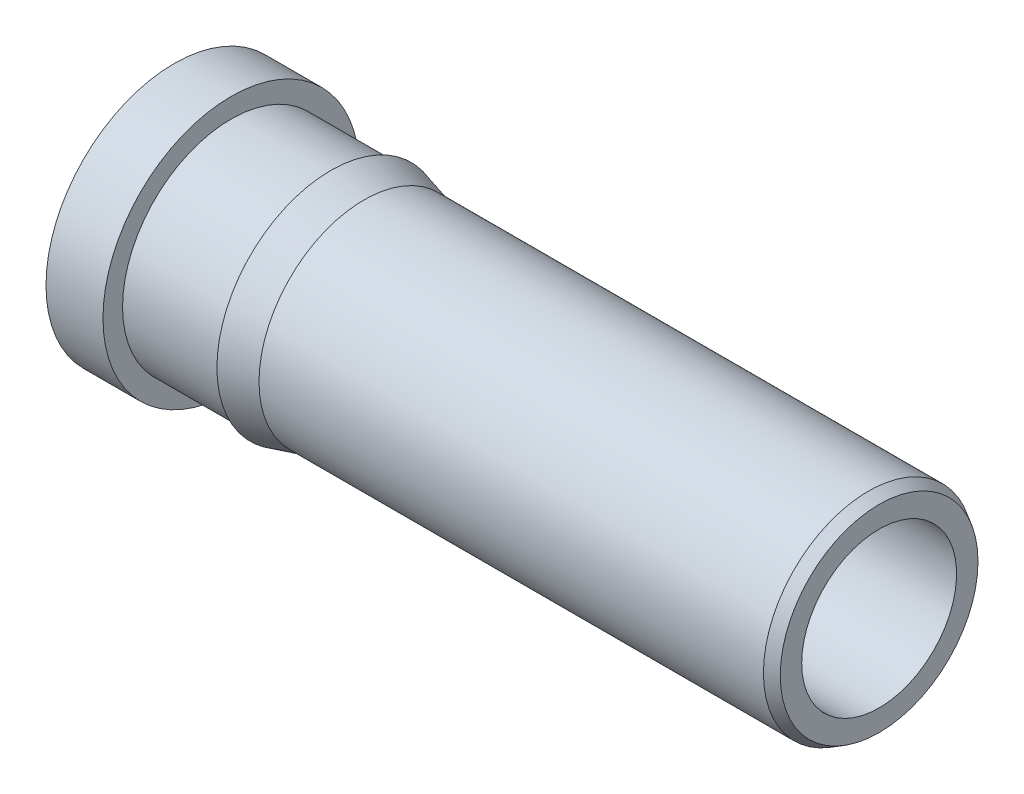
SolidWorks part; units mm, degrees
material "Brass Alloy 385"
ref_plane "Front Plane" through (0, 0, 0) normal (0, 0, 1) x (1, 0, 0)
ref_plane "Top Plane" through (0, 0, 0) normal (0, 1, 0) x (1, 0, 0)
ref_plane "Right Plane" through (0, 0, 0) normal (1, 0, 0) x (0, 0, -1)
sketch "Sketch1" plane through (0, 0, 0) normal (0, 0, 1) x (1, 0, 0)
  line L0 (0, 0) -> (0, 0.9144)
  line L1 (0, 0.9144) -> (0.4064, 0.9144)
  line L2 (0.4064, 0.9144) -> (0.4064, 0.7747)
  line L3 (0.4064, 0.7747) -> (1.1176, 0.7747)
  line L4 (1.1176, 0.7747) -> (1.1176, 0.8128)
  line L5 (1.1176, 0.8128) -> (1.3546, 0.7493)
  line L6 (1.3546, 0.7493) -> (4.953, 0.7493)
  line L7 (4.953, 0.7493) -> (5.0292, 0.7053)
  line L8 (5.0292, 0.7053) -> (5.0292, 0)
  line L9 (0, 0) -> (5.0292, 0)
  line L10 (0, 0) -> (5.0292, 0) construction
revolve "RevolutionAngle1" add sketch "Sketch1" angle 360 about L10
hole_wizard "Hole1" positions "Sketch3" profile "Sketch2" legacy
sketch "Sketch3" plane through (0, 0, 0) normal (-1, 0, 0) x (0, 0, 1)
  point P0 (0, 0)
sketch "Sketch2" plane through (0, 0, 0) normal (0, 1, 0) x (0, 0, 1)
  line L0 (0, 0) -> (0, 2.726)
  line L1 (0, 2.726) -> (0.6477, 2.3368)
  line L2 (0.6477, 2.3368) -> (0.6477, 0)
  line L4 (0.6477, 0) -> (0, 0)
  line L6 (0, 2.726) -> (-0.6477, 2.3368) construction
  line L7 (0, -4.2442) -> (0, 117.3081) construction
  dimension "Diameter" = 1.2954
  dimension "Depth" = 2.3368
  dimension "Drill Angle" = 118
hole_wizard "Hole2" positions "Sketch5" profile "Sketch4" legacy end condition through all
sketch "Sketch5" plane through (0, 0.3419, -0.6852) normal (-1, 0, 0) x (0, 0, 1)
  point P0 (0.6852, -0.3419)
sketch "Sketch4" plane through (0, 0, 0) normal (0, 1, 0) x (0, 0, 1)
  line L0 (0, 0) -> (0, 5.3611)
  line L1 (0, 5.3611) -> (0.5524, 5.0292)
  line L2 (0.5524, 5.0292) -> (0.5524, 0)
  line L4 (0.5524, 0) -> (0, 0)
  line L6 (0, 5.3611) -> (-0.5524, 5.0292) construction
  line L7 (0, -4.2442) -> (0, 117.3081) construction
  dimension "Diameter" = 1.1049
  dimension "Depth" = 5.0292
  dimension "Drill Angle" = 118
